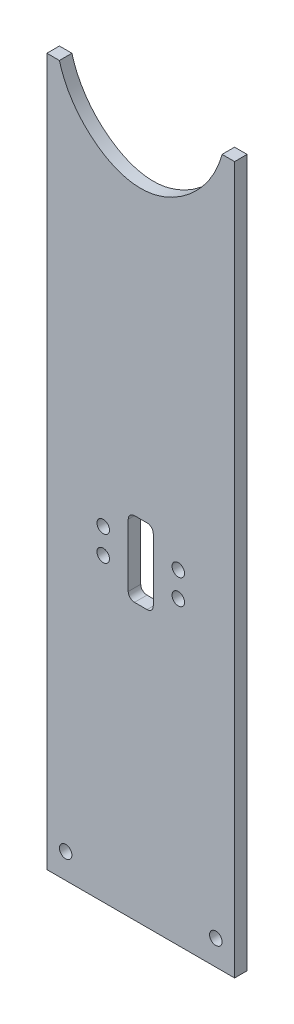
SolidWorks part; units mm, degrees
ref_plane "Front Plane" through (0, 0, 0) normal (0, 0, 1) x (1, 0, 0)
ref_plane "Top Plane" through (0, 0, 0) normal (0, 1, 0) x (1, 0, 0)
ref_plane "Right Plane" through (0, 0, 0) normal (1, 0, 0) x (0, 0, -1)
sketch "Sketch1" plane through (0, 0, 0) normal (0, 0, 1) x (1, 0, 0)
  line L1 (0, 0) -> (95.25, 0)
  line L2 (0, 0) -> (0, 406.4)
  line L3 (0, 406.4) -> (95.25, 406.4)
  line L4 (95.25, 0) -> (95.25, 406.4)
  dimension "D1" = 95.25
  dimension "D2" = 406.4
extrude "Boss-Extrude1" add sketch "Sketch1" along normal blind 6.35
sketch3d "3DSketch1"
  spline S0 degree 3 poles (472.3078, 2273.3921, 0) (234.4327, 516.8543, 0) (109.5518, 299.6231, 0) (35.5652, 327.2199, 0) (34.5818, 327.6367, 0) (31.6902, 328.9986, 0) (29.8403, 330.054, 0) (27.6134, 331.5354, 0) (27.1721, 331.8401, 0) (26.304, 332.4613, 0) (25.8763, 332.7785, 0) (24.6116, 333.7487, 0) (23.7929, 334.4208, 0) (21.4078, 336.5093, 0) (19.9114, 337.9977, 0) (17.8061, 340.3733, 0) (17.1277, 341.1891, 0) (15.8188, 342.8699, 0) (15.1871, 343.7369, 0) (13.3915, 346.3766, 0) (12.3179, 348.1977, 0) (10.4172, 351.9621, 0) (9.5901, 353.9055, 0) (8.7184, 356.4152, 0) (8.5522, 356.9211, 0) (8.2365, 357.9413, 0) (8.0868, 358.4562, 0) (7.6666, 360.0008, 0) (7.4236, 361.0345, 0) (6.8047, 364.1473, 0) (6.5382, 366.238, 0) (6.3608, 369.3977, 0) (6.3389, 370.4548, 0) (6.3634, 372.0467, 0) (6.3812, 372.5783, 0) (6.4363, 373.6436, 0) (6.4737, 374.1785, 0) (6.7093, 376.8415, 0) (7.0509, 378.9323, 0) (8.0334, 383.0364, 0) (8.6742, 385.0498, 0) (9.6695, 387.5163, 0) (9.8783, 388.0071, 0) (10.3159, 388.9834, 0) (10.5444, 389.4685, 0) (11.254, 390.9032, 0) (11.7607, 391.8364, 0) (13.3796, 394.5677, 0) (14.5903, 396.2979, 0) (16.6058, 398.7554, 0) (17.3109, 399.5515, 0) (18.4204, 400.7101, 0) (18.7991, 401.0905, 0) (19.5671, 401.8325, 0) (19.9572, 402.1951, 0) (134.611, 504.7144, 0) (745.4771, -87.0679, 0) (1522.2798, -910.7259, 0) knots -2.236942 -2.236942 -2.236942 -2.236942 0.03125 0.03125 0.0625 0.0625 0.125 0.125 0.140625 0.140625 0.15625 0.15625 0.1875 0.1875 0.25 0.25 0.28125 0.28125 0.3125 0.3125 0.375 0.375 0.4375 0.4375 0.453125 0.453125 0.46875 0.46875 0.5 0.5 0.5625 0.5625 0.59375 0.59375 0.609375 0.609375 0.625 0.625 0.6875 0.6875 0.75 0.75 0.765625 0.765625 0.78125 0.78125 0.8125 0.8125 0.875 0.875 0.90625 0.90625 0.921875 0.921875 0.9375 0.9375 5.444978 5.444978 5.444978 5.444978 only from (39.6169, 325.8623, 0) to (25.3916, 406.4, 0)
  spline S1 degree 3 poles (1812.7793, 1278.5615, 0) (-48.2451, 365.4179, 0) (18.9237, 313.9619, 0) (57.6813, 326.4848, 0) (58.185, 326.6604, 0) (59.6806, 327.2185, 0) (60.6567, 327.6319, 0) (63.529, 328.983, 0) (65.3696, 330.0305, 0) (68.0319, 331.7968, 0) (68.9047, 332.4203, 0) (70.5952, 333.714, 0) (71.4154, 334.3859, 0) (73.8047, 336.4734, 0) (75.3025, 337.9604, 0) (77.4087, 340.3319, 0) (78.0872, 341.1461, 0) (79.396, 342.8227, 0) (80.0282, 343.6882, 0) (81.829, 346.3288, 0) (82.9063, 348.1514, 0) (84.8145, 351.9213, 0) (85.6455, 353.8686, 0) (86.6967, 356.8881, 0) (87.0145, 357.9124, 0) (87.5744, 359.9649, 0) (87.8179, 360.9966, 0) (88.4393, 364.1081, 0) (88.7089, 366.2042, 0) (88.8888, 369.3818, 0) (88.9113, 370.4473, 0) (88.8782, 372.5874, 0) (88.8229, 373.6505, 0) (88.5429, 376.8196, 0) (88.2044, 378.9053, 0) (87.4669, 381.9929, 0) (87.1826, 383.0153, 0) (86.5349, 385.0459, 0) (86.1703, 386.0561, 0) (84.9741, 389.0161, 0) (84.0363, 390.9117, 0) (82.4211, 393.6396, 0) (81.8478, 394.5296, 0) (80.9345, 395.835, 0) (80.6211, 396.2652, 0) (79.9763, 397.1156, 0) (79.6441, 397.5366, 0) (77.9494, 399.6013, 0) (76.4829, 401.1298, 0) (-2.1063, 471.4564, 0) (-336.875, 253.6007, 0) (-1473.8076, -856.7333, 0) knots -1.157672 -1.157672 -1.157672 -1.157672 0.015625 0.015625 0.03125 0.03125 0.0625 0.0625 0.125 0.125 0.15625 0.15625 0.1875 0.1875 0.25 0.25 0.28125 0.28125 0.3125 0.3125 0.375 0.375 0.4375 0.4375 0.46875 0.46875 0.5 0.5 0.5625 0.5625 0.59375 0.59375 0.625 0.625 0.6875 0.6875 0.71875 0.71875 0.75 0.75 0.8125 0.8125 0.84375 0.84375 0.859375 0.859375 0.875 0.875 0.9375 0.9375 3.995182 3.995182 3.995182 3.995182 only from (55.6331, 325.8623, 0) to (69.8584, 406.4, 0)
  spline S2 degree 3 poles (39.6169, 325.8623, 0) (38.5916, 326.1412, 0) (37.5762, 326.4698, 0) (35.5652, 327.2199, 0) (34.5818, 327.6367, 0) (31.6902, 328.9986, 0) (29.8403, 330.054, 0) (27.6134, 331.5354, 0) (27.1721, 331.8401, 0) (26.304, 332.4613, 0) (25.8763, 332.7785, 0) (24.6116, 333.7487, 0) (23.7929, 334.4208, 0) (21.4078, 336.5093, 0) (19.9114, 337.9977, 0) (17.8061, 340.3733, 0) (17.1277, 341.1891, 0) (15.8188, 342.8699, 0) (15.1871, 343.7369, 0) (13.3915, 346.3766, 0) (12.3179, 348.1977, 0) (10.4172, 351.9621, 0) (9.5901, 353.9055, 0) (8.7184, 356.4152, 0) (8.5522, 356.9211, 0) (8.2365, 357.9413, 0) (8.0868, 358.4562, 0) (7.6666, 360.0008, 0) (7.4236, 361.0345, 0) (6.8047, 364.1473, 0) (6.5382, 366.238, 0) (6.3608, 369.3977, 0) (6.3389, 370.4548, 0) (6.3634, 372.0467, 0) (6.3812, 372.5783, 0) (6.4363, 373.6436, 0) (6.4737, 374.1785, 0) (6.7093, 376.8415, 0) (7.0509, 378.9323, 0) (8.0334, 383.0364, 0) (8.6742, 385.0498, 0) (9.6695, 387.5163, 0) (9.8783, 388.0071, 0) (10.3159, 388.9834, 0) (10.5444, 389.4685, 0) (11.254, 390.9032, 0) (11.7607, 391.8364, 0) (13.3796, 394.5677, 0) (14.5903, 396.2979, 0) (16.6058, 398.7554, 0) (17.3109, 399.5515, 0) (18.4204, 400.7101, 0) (18.7991, 401.0905, 0) (19.5671, 401.8325, 0) (19.9572, 402.1951, 0) (21.9375, 403.9658, 0) (23.6173, 405.249, 0) (25.3916, 406.4, 0) knots 0 0 0 0 0.03125 0.03125 0.0625 0.0625 0.125 0.125 0.140625 0.140625 0.15625 0.15625 0.1875 0.1875 0.25 0.25 0.28125 0.28125 0.3125 0.3125 0.375 0.375 0.4375 0.4375 0.453125 0.453125 0.46875 0.46875 0.5 0.5 0.5625 0.5625 0.59375 0.59375 0.609375 0.609375 0.625 0.625 0.6875 0.6875 0.75 0.75 0.765625 0.765625 0.78125 0.78125 0.8125 0.8125 0.875 0.875 0.90625 0.90625 0.921875 0.921875 0.9375 0.9375 1 1 1 1
  spline S4 degree 3 poles (55.6331, 325.8623, 0) (56.1481, 326.0024, 0) (56.6626, 326.1556, 0) (57.6813, 326.4848, 0) (58.185, 326.6604, 0) (59.6806, 327.2185, 0) (60.6567, 327.6319, 0) (63.529, 328.983, 0) (65.3696, 330.0305, 0) (68.0319, 331.7968, 0) (68.9047, 332.4203, 0) (70.5952, 333.714, 0) (71.4154, 334.3859, 0) (73.8047, 336.4734, 0) (75.3025, 337.9604, 0) (77.4087, 340.3319, 0) (78.0872, 341.1461, 0) (79.396, 342.8227, 0) (80.0282, 343.6882, 0) (81.829, 346.3288, 0) (82.9063, 348.1514, 0) (84.8145, 351.9213, 0) (85.6455, 353.8686, 0) (86.6967, 356.8881, 0) (87.0145, 357.9124, 0) (87.5744, 359.9649, 0) (87.8179, 360.9966, 0) (88.4393, 364.1081, 0) (88.7089, 366.2042, 0) (88.8888, 369.3818, 0) (88.9113, 370.4473, 0) (88.8782, 372.5874, 0) (88.8229, 373.6505, 0) (88.5429, 376.8196, 0) (88.2044, 378.9053, 0) (87.4669, 381.9929, 0) (87.1826, 383.0153, 0) (86.5349, 385.0459, 0) (86.1703, 386.0561, 0) (84.9741, 389.0161, 0) (84.0363, 390.9117, 0) (82.4211, 393.6396, 0) (81.8478, 394.5296, 0) (80.9345, 395.835, 0) (80.6211, 396.2652, 0) (79.9763, 397.1156, 0) (79.6441, 397.5366, 0) (77.9494, 399.6013, 0) (76.4829, 401.1298, 0) (73.3345, 403.9472, 0) (71.6526, 405.2361, 0) (69.8584, 406.4, 0) knots 0 0 0 0 0.015625 0.015625 0.03125 0.03125 0.0625 0.0625 0.125 0.125 0.15625 0.15625 0.1875 0.1875 0.25 0.25 0.28125 0.28125 0.3125 0.3125 0.375 0.375 0.4375 0.4375 0.46875 0.46875 0.5 0.5 0.5625 0.5625 0.59375 0.59375 0.625 0.625 0.6875 0.6875 0.71875 0.71875 0.75 0.75 0.8125 0.8125 0.84375 0.84375 0.859375 0.859375 0.875 0.875 0.9375 0.9375 1 1 1 1
sketch "Sketch2" plane through (0, 0, 0) normal (0, 0, -1) x (-1, 0, 0)
  line L0 (-95.25, 358.7951) -> (-88.8999, 358.7951)
  line L1 (0, 358.7954) -> (-6.35, 358.7954)
  line L3 (-95.25, 0) -> (-95.25, 406.4) construction
  line L4 (0, 406.4) -> (0, 0) construction
  line L6 (-95.25, 358.7951) -> (-95.25, 406.4)
  line L7 (-95.25, 406.4) -> (0, 406.4)
  line L8 (0, 406.4) -> (0, 358.7954)
  spline S1 degree 3 poles (-88.8999, 358.7951) (-88.7469, 358.2209) (-87.9814, 355.5481) (-86.1567, 350.7761) (-82.7934, 344.6593) (-78.5537, 339.0004) (-73.5683, 333.9404) (-67.9028, 329.602) (-61.7599, 326.1752) (-56.0113, 324.164) (-51.2742, 323.327) (-47.6264, 323.1063) (-43.9648, 323.3277) (-39.2301, 324.1679) (-33.493, 326.1665) (-27.1993, 329.6965) (-19.7537, 335.4384) (-13.5095, 342.7204) (-9.0915, 350.7818) (-7.3614, 355.3209) (-6.5828, 357.9431) (-6.4258, 358.511) (-6.35, 358.7954) knots 0.244654 0.244654 0.244654 0.244654 0.252466 0.28125 0.3125 0.34375 0.375 0.40625 0.4375 0.46875 0.484375 0.5 0.515625 0.53125 0.5625 0.59375 0.625 0.6875 0.71875 0.747082 0.750988 0.754895 0.754895 0.754895 0.754895
extrude "Cut-Extrude1" cut sketch "Sketch2" against normal blind 6.35
sketch "Sketch3" plane through (0, 0, 0) normal (0, 0, -1) x (-1, 0, 0)
  line L0 (0, 358.7954) -> (0, 0) construction
  line L1 (-50.8, 177.8) -> (-44.45, 177.8)
  line L2 (-53.975, 174.625) -> (-53.975, 142.875)
  line L3 (-50.8, 139.7) -> (-44.45, 139.7)
  line L4 (-41.275, 174.625) -> (-41.275, 142.875)
  line L5 (0, 0) -> (-95.25, 0) construction
  line L7 (-10.2753, 158.75) -> (-80.2273, 158.75) construction
  circle A0 centre (-28.575, 165.1) radius 3.175
  circle A1 centre (-66.675, 165.1) radius 3.175
  circle A2 centre (-66.675, 152.4) radius 3.175
  circle A3 centre (-28.575, 152.4) radius 3.175
  arc A4 (-53.975, 142.875) -> (-50.8, 139.7) centre (-50.8, 142.875) ccw
  arc A5 (-44.45, 139.7) -> (-41.275, 142.875) centre (-44.45, 142.875) ccw
  arc A6 (-44.45, 177.8) -> (-41.275, 174.625) centre (-44.45, 174.625) cw
  arc A7 (-50.8, 177.8) -> (-53.975, 174.625) centre (-50.8, 174.625) ccw
  point P20 (-53.975, 139.7)
  point P27 (-53.975, 177.8)
  dimension "D5" = 6.35
  dimension "D6" = 6.35
  dimension "D7" = 6.35
  dimension "D8" = 6.35
  dimension "D9" = 12.7
  dimension "D10" = 12.7
  dimension "D11" = 3.175
  dimension "D1" = 12.7
  dimension "D2" = 41.275
  dimension "D3" = 38.1
  dimension "D4" = 139.7
extrude "Cut-Extrude2" cut sketch "Sketch3" against normal blind 6.35
sketch "Sketch4" plane through (0, 0, 0) normal (0, 0, -1) x (-1, 0, 0)
  line L0 (-95.25, 0) -> (-95.25, 358.7951) construction
  line L1 (0, 358.7954) -> (0, 0) construction
  line L2 (0, 0) -> (-95.25, 0) construction
  circle A0 centre (-9.525, 12.7) radius 3.175
  circle A1 centre (-85.725, 12.7) radius 3.175
  dimension "D1" = 9.525
  dimension "D2" = 9.525
  dimension "D3" = 12.7
  dimension "D4" = 12.7
  dimension "D5" = 6.35
  dimension "D6" = 6.35
extrude "Cut-Extrude3" cut sketch "Sketch4" against normal through all
